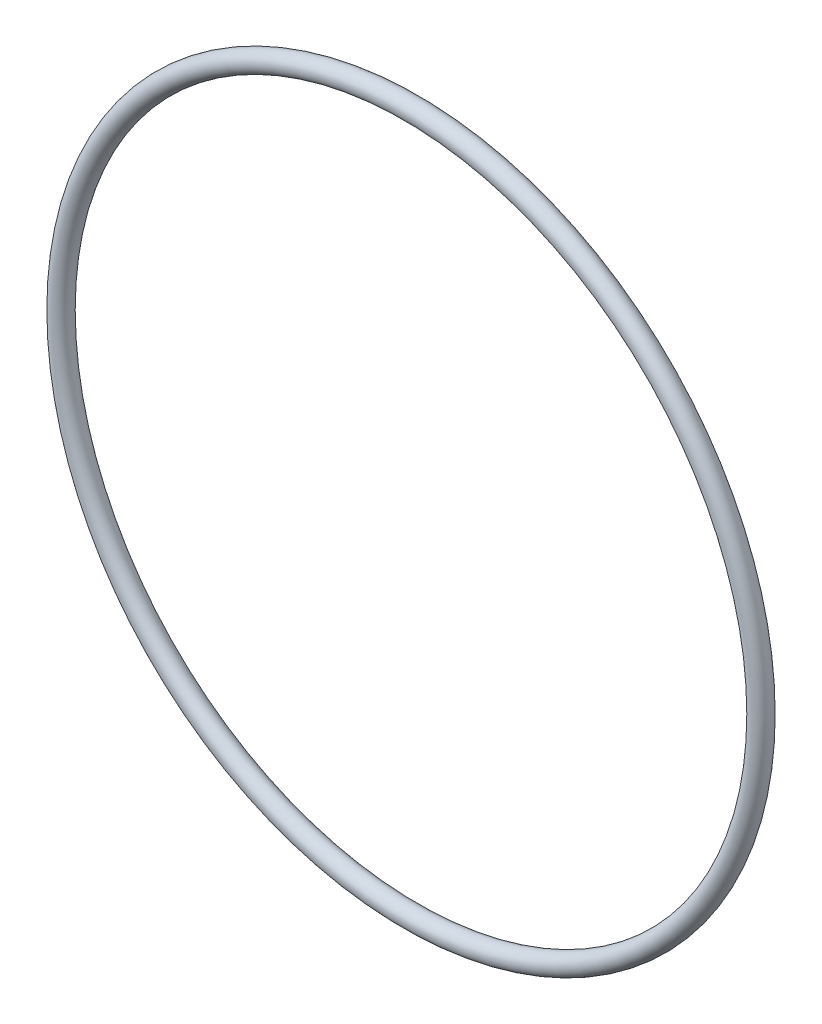
SolidWorks part; units mm, degrees
ref_plane "Front" through (0, 0, 0) normal (0, 0, 1) x (1, 0, 0)
ref_plane "Top" through (0, 0, 0) normal (0, 1, 0) x (1, 0, 0)
ref_plane "Right" through (0, 0, 0) normal (1, 0, 0) x (0, 0, -1)
sketch "Sketch1" plane through (0, 0, 0) normal (1, 0, 0) x (0, -1, 0)
  line L0 (0, -1.3081) -> (0, 1.3081) construction
  line L2 (-51.5912, 0) -> (51.5912, 0) construction
  line L3 (-44.2849, 0) -> (44.2849, 0) construction
  circle A0 centre (45.593, 0) radius 1.3081
  point P9 (44.2849, 0)
  point P10 (46.9011, 0)
  point P13 (45.593, 1.3081)
  point P14 (45.593, -1.3081)
  dimension "Width" = 2.6162
  dimension "ID" = 88.5698
revolve "Revolve1" add sketch "Sketch1" angle 360 about L0
